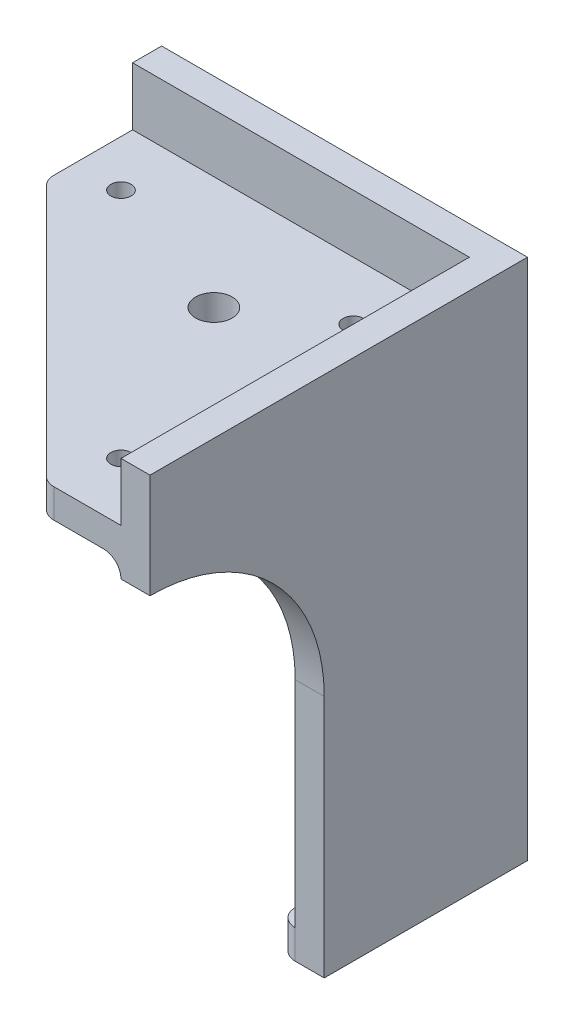
SolidWorks part; units mm, degrees
ref_plane "Alzado" through (0, 0, 0) normal (0, 0, 1) x (1, 0, 0)
ref_plane "Planta" through (0, 0, 0) normal (0, 1, 0) x (1, 0, 0)
ref_plane "Vista lateral" through (0, 0, 0) normal (1, 0, 0) x (0, 0, -1)
sketch "Croquis1" plane through (0, 0, 0) normal (0, 0, 1) x (1, 0, 0)
  line L0 (-63, 0) -> (0, 0)
  line L1 (0, 0) -> (0, -90)
  line L2 (0, -90) -> (-33, -90)
  line L3 (-33, -90) -> (-33, -48)
  line L6 (-63, -18) -> (-63, 0)
  arc A0 (-33, -48) -> (-63, -18) centre (-63, -48) ccw
  dimension "D1" = 60
  dimension "D2" = 33
  dimension "D3" = 90
  dimension "D4" = 63
  dimension "D5" = 42
extrude "Saliente-Extruir1" add sketch "Croquis1" along normal blind 5 separate body
sketch "Croquis2" plane through (0, 0, 5) normal (0, 0, 1) x (1, 0, 0)
  line L1 (0, 0) -> (-5, 0)
  line L2 (0, 0) -> (0, -90)
  line L3 (0, -90) -> (-5, -90)
  line L4 (-5, 0) -> (-5, -90)
  line L5 (0, -90) -> (0, 0) construction
  line L6 (0, 0) -> (-63, 0) construction
  line L7 (-33, -90) -> (0, -90) construction
  dimension "D1" = 5
extrude "Saliente-Extruir2" add sketch "Croquis2" along normal blind 60
sketch "Croquis3" plane through (0, 0, 0) normal (1, 0, 0) x (0, 0, -1)
  line L0 (-65, -90) -> (-35, -90)
  line L1 (-35, -90) -> (-35, -48)
  line L2 (-65, -90) -> (-65, -18)
  line L3 (-65, -90) -> (-65, 0) construction
  line L4 (-65, -90) -> (0, -90) construction
  arc A0 (-35, -48) -> (-65, -18) centre (-65, -48) ccw
  dimension "D3" = 60
  dimension "D1" = 30
  dimension "D2" = 72
extrude "Cortar-Extruir1" cut sketch "Croquis3" against normal up to surface (5 mm away) up to face at (-5, -33.75, 50)
sketch "Croquis4" plane through (0, -90, 0) normal (0, -1, 0) x (1, 0, 0)
  line L0 (-33, 8) -> (-8, 8)
  line L1 (-33, 5) -> (-5, 5)
  line L2 (-33, 5) -> (-33, 8)
  line L3 (-8, 35) -> (-5, 35)
  line L4 (-5, 5) -> (-5, 35)
  line L5 (-8, 8) -> (-8, 35)
  line L6 (-33, 5) -> (-5, 5) construction
  line L7 (-5, 35) -> (-5, 5) construction
  line L8 (-5, 35) -> (0, 35) construction
  line L9 (-33, 5) -> (-33, 0) construction
  dimension "D1" = 3
extrude "Saliente-Extruir3" add sketch "Croquis4" against normal blind 5
fillet "Redondeo1" radius 3 2 edges at (-33, -87.5, 8) (-8, -87.5, 35)
sketch "Croquis5" plane through (0, 0, 5) normal (0, 0, 1) x (1, 0, 0)
  line L0 (-5, 0) -> (-63, 0) construction
  line L1 (-5, -10) -> (-63, -10)
  line L2 (-5, -10) -> (-5, -15)
  line L3 (-5, -15) -> (-63, -15)
  line L4 (-63, -10) -> (-63, -15)
  line L6 (-63, 0) -> (-63, -18) construction
  line L7 (-5, 0) -> (-5, -85) construction
  dimension "D1" = 10
  dimension "D2" = 5
extrude "Saliente-Extruir4" add sketch "Croquis5" along normal up to surface (60 mm away) up to face at (-2.5, -9, 65)
sketch "Croquis6" plane through (0, -10, 0) normal (0, 1, 0) x (1, 0, 0)
  line L0 (-63, -19.8176) -> (-17.8176, -65)
  line L1 (-63, -65) -> (-63, -5) construction
  line L2 (-63, -65) -> (-5, -65) construction
  line L3 (-17.8176, -65) -> (-63, -65)
  line L4 (-63, -65) -> (-63, -19.8176)
  line L5 (-5, -5) -> (-63, -5) construction
  line L6 (-5, -65) -> (-5, -5) construction
  circle A0 centre (-60, -18.575) radius 3 construction
  dimension "D3" = 6
  dimension "D1" = 13.575
  dimension "D2" = 45
extrude "Cortar-Extruir2" cut sketch "Croquis6" against normal up to surface (5 mm away) up to face at (-34, -15, 35)
fillet "Redondeo2" radius 3 2 edges at (-17.8176, -12.5, 65) (-63, -12.5, 19.8176)
fillet "Redondeo3" radius 3 3 edges at (-34, -15, 5) (-5, -15, 35)
sketch "Croquis7" plane through (0, -10, 0) normal (0, 1, 0) x (1, 0, 0)
  line L0 (-5, -5) -> (-63, -5) construction
  line L1 (-5, -65) -> (-5, -5) construction
  circle A0 centre (-15, -55) radius 1.75
  circle A1 centre (-15, -15) radius 1.75
  circle A2 centre (-55, -15) radius 1.75
  circle A3 centre (-29.5, -24.5) radius 3.15
  dimension "D1" = 3.5
  dimension "D2" = 40
  dimension "D3" = 40
  dimension "D4" = 10
  dimension "D5" = 10
  dimension "D6" = 6.3
extrude "Cortar-Extruir3" cut sketch "Croquis7" against normal up to surface (5 mm away) up to face at (-34.2416, -15, 35.6701)
